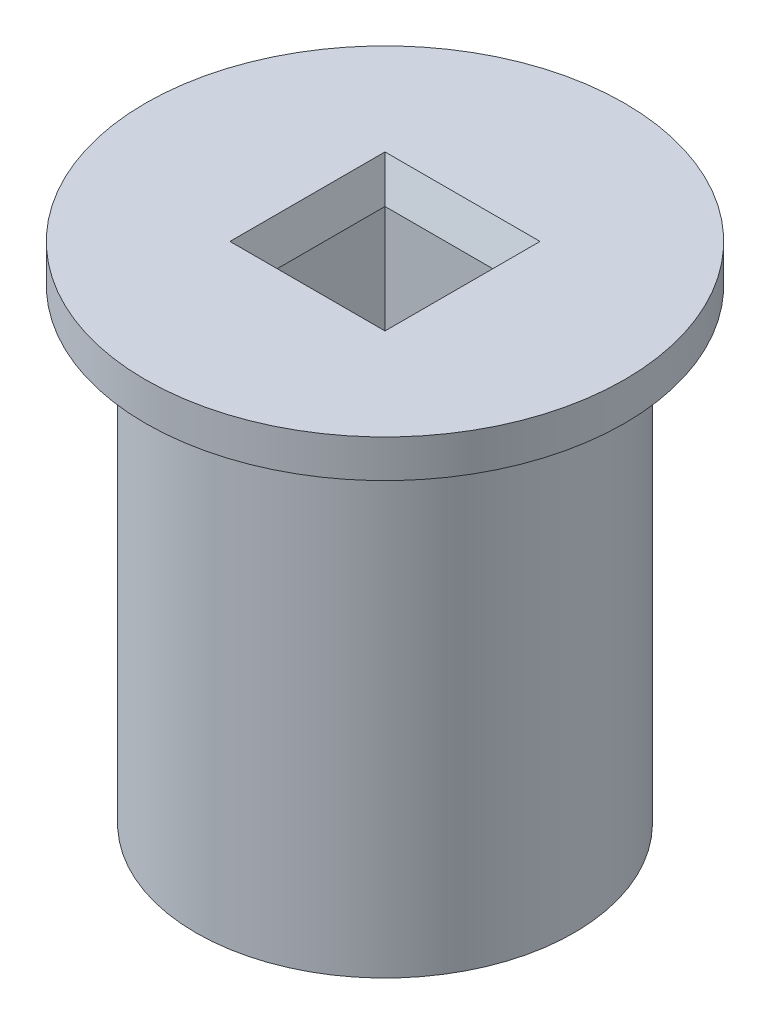
SolidWorks part; units mm, degrees
ref_plane "Спереди" through (0, 0, 0) normal (0, 0, 1) x (1, 0, 0)
ref_plane "Сверху" through (0, 0, 0) normal (0, 1, 0) x (1, 0, 0)
ref_plane "Справа" through (0, 0, 0) normal (1, 0, 0) x (0, 0, -1)
sketch "Эскиз1" plane through (0, 0, 0) normal (0, 1, 0) x (1, 0, 0)
  line L1 (5.15, -5.15) -> (-5.15, -5.15)
  line L2 (5.15, -5.15) -> (5.15, 5.15)
  line L3 (5.15, 5.15) -> (-5.15, 5.15)
  line L4 (-5.15, -5.15) -> (-5.15, 5.15)
  line L5 (5.15, -5.15) -> (-5.15, 5.15) construction
  line L6 (5.15, 5.15) -> (-5.15, -5.15) construction
  circle A0 centre (0, 0) radius 15
  dimension "D1" = 30
  dimension "D2" = 10.3
extrude "Бобышка-Вытянуть1" add sketch "Эскиз1" along normal blind 40
sketch "Sketch1" plane through (0, 40, 0) normal (0, 1, 0) x (1, 0, 0)
  line L1 (5.15, -5.15) -> (-5.15, -5.15)
  line L2 (5.15, -5.15) -> (5.15, 5.15)
  line L3 (5.15, 5.15) -> (-5.15, 5.15)
  line L4 (-5.15, -5.15) -> (-5.15, 5.15)
  line L5 (5.15, -5.15) -> (-5.15, 5.15) construction
  line L6 (5.15, 5.15) -> (-5.15, -5.15) construction
  circle A0 centre (0, 0) radius 19
  dimension "D1" = 38
extrude "Boss-Extrude1" add sketch "Sketch1" against normal blind 3
chamfer "Chamfer1" distance 1 angle 70 4 edges at (5.15, 40, 0) (0, 40, 5.15) (-5.15, 40, 0) (0, 40, -5.15)
